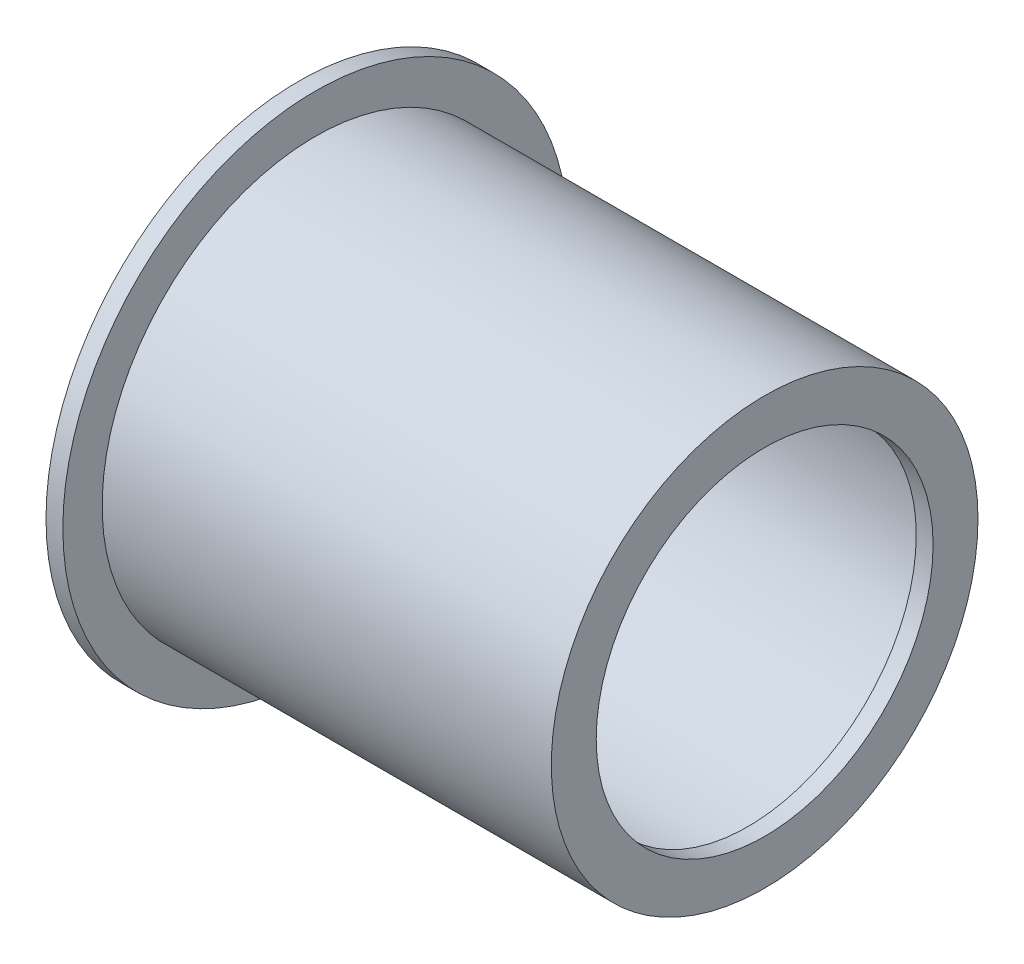
SolidWorks part; units mm, degrees
ref_plane "Front Plane" through (0, 0, 0) normal (0, 0, 1) x (1, 0, 0)
ref_plane "Top Plane" through (0, 0, 0) normal (0, 1, 0) x (1, 0, 0)
ref_plane "Right Plane" through (0, 0, 0) normal (1, 0, 0) x (0, 0, -1)
sketch "Sketch1" plane through (0, 0, 0) normal (0, 0, 1) x (1, 0, 0)
  line L0 (-80, 45) -> (-80, 35)
  line L1 (-80, 35) -> (0, 35)
  line L2 (0, 35) -> (0, 30)
  line L3 (0, 0) -> (-84.6271, 0) construction
  dimension "D1" = 80
  dimension "D2" = 10
  dimension "D3" = 5
  dimension "D4" = 35
revolve "Revolve-Thin1" add sketch "Sketch1" angle 360 about L3 wall 3
sketch "Sketch2" plane through (-80, 0, 0) normal (-1, 0, 0) x (0, 0, 1)
  circle A0 centre (0, 0) radius 35
extrude "Boss-Extrude1" add sketch "Sketch2" against normal blind 3
